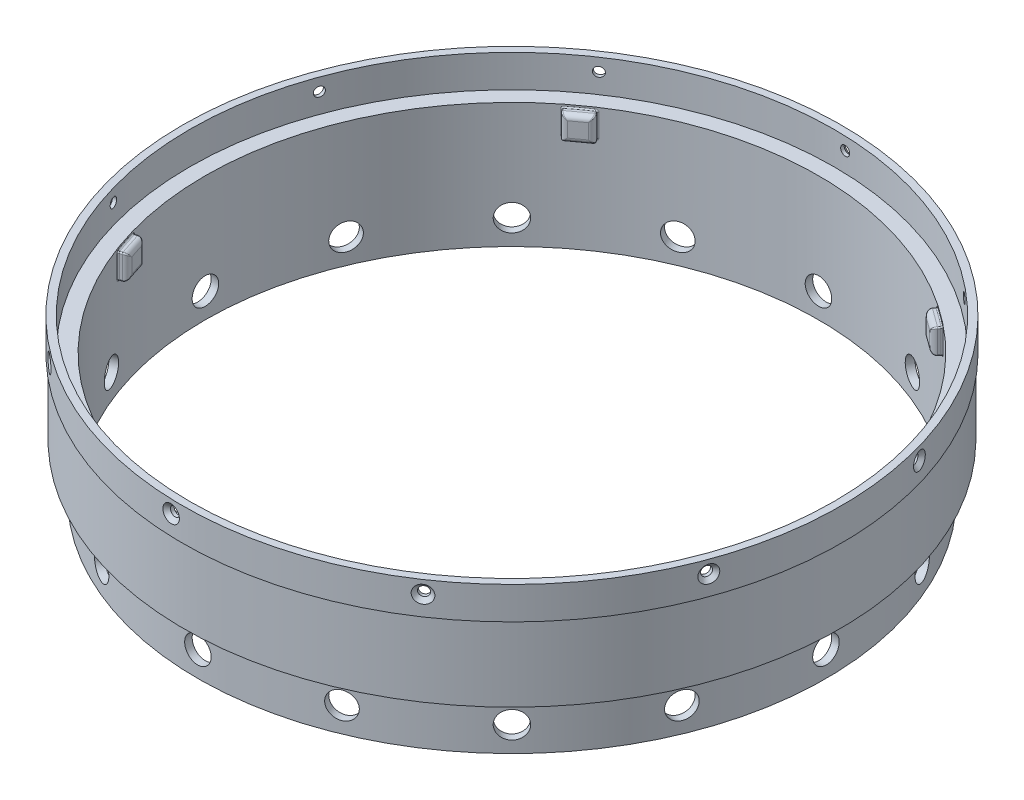
SolidWorks part; units mm, degrees
ref_plane "Front Plane" through (0, 0, 0) normal (0, 0, 1) x (1, 0, 0)
ref_plane "Top Plane" through (0, 0, 0) normal (0, 1, 0) x (1, 0, 0)
ref_plane "Right Plane" through (0, 0, 0) normal (1, 0, 0) x (0, 0, -1)
sketch "Sketch1" plane through (0, 0, 0) normal (0, 0, 1) x (1, 0, 0)
  line L0 (0, 49.1435) -> (0, -38.5417) construction
  line L1 (83.82, 42.3241) -> (83.82, 34.0691)
  line L2 (83.82, 34.0691) -> (83.439, 34.0691)
  line L3 (83.439, 34.0691) -> (83.439, 15.0191)
  line L4 (83.439, 15.0191) -> (79.9338, 15.0191)
  line L5 (79.9338, 15.0191) -> (79.9338, 2.3191)
  line L6 (79.9338, 2.3191) -> (78.0288, 2.3191)
  line L7 (78.0288, 2.3191) -> (78.0288, 34.0691)
  line L8 (78.0288, 34.0691) -> (81.9531, 34.0691)
  line L9 (81.9531, 34.0691) -> (81.9531, 42.3241)
  line L10 (81.9531, 42.3241) -> (83.82, 42.3241)
  point P15 (0, 0)
  dimension "D1" = 19.05
  dimension "D2" = 0.381
  dimension "D3" = 8.255
  dimension "D4" = 31.75
  dimension "D5" = 12.7
  dimension "D6" = 1.8669
  dimension "D7" = 1.905
  dimension "D8" = 83.82
  dimension "D9" = 3.5052
revolve "Revolve1" add sketch "Sketch1" angle 360 about L0
hole_wizard "CSK for M2 Flat Head Machine Screw1" positions "3DSketch2" profile "Sketch2" countersink size "M2" standard "ANSI Metric" end condition through all
sketch3d "3DSketch2"
  point P0 (80.574, 39.0781, -23.1003)
sketch "Sketch2" plane through (80.574, 39.0781, -23.1003) normal (0, 1, 0) x (-0.2756, 0, -0.9613)
  line L0 (0, 0) -> (0, 201.4765)
  line L1 (0, 201.4765) -> (1.2, 201.4765)
  line L2 (1.2, 201.4765) -> (1.2, 1)
  line L3 (1.2, 1) -> (2.2, 0)
  line L5 (2.2, 0) -> (0, 0)
  line L6 (-1.2, 1) -> (-2.2, 0) construction
  line L11 (0, -6.35) -> (0, 107.95) construction
  dimension "Thru Hole Dia." = 2.4
  dimension "Thru Hole Depth" = 201.4765
  dimension "Near C'Sink Dia." = 4.4
  dimension "Near C'Sink Angle" = 90
pattern_circular "CirPattern1" count 10 over 360 about axis through (0, 49.1435, 0) along (0, 1, 0) of "CSK for M2 Flat Head Machine Screw1"
sketch3d "3DSketch4"
  point P0 (-2.4273, 4.97, 79.8969)
ref_plane "Plane1" through (0, 0, 82.4369) normal (0, 0, 1) x (1, 0, 0)
hole_wizard "17/64 (0.26563) Diameter Hole1" positions "Sketch6" profile "Sketch7" hole size "17/64" standard "ANSI Inch" end condition through all
sketch "Sketch6" plane through (0, 0, 82.4369) normal (0, 0, 1) x (1, 0, 0)
  line L0 (-79.9338, 15.0191) -> (79.9338, 15.0191) construction
  point P0 (0, 8.6691)
  dimension "D1" = 6.35
sketch "Sketch7" plane through (0, 8.6691, 82.4369) normal (1, 0, 0) x (0, -1, 0)
  line L0 (0, 0) -> (0, 191.953)
  line L1 (0, 191.953) -> (3.3735, 191.953)
  line L2 (3.3735, 191.953) -> (3.3735, 0)
  line L5 (3.3735, 0) -> (0, 0)
  line L11 (0, -6.35) -> (0, 107.95) construction
  dimension "Thru Hole Dia." = 6.747
  dimension "Thru Hole Depth" = 191.953
pattern_circular "CirPattern2" count 16 over 360 about axis through (0, 49.1435, 0) along (0, 1, 0) of "17/64 (0.26563) Diameter Hole1"
ref_plane "Plane3" through (0, 0, 80.518) normal (0, 0, 1) x (1, 0, 0)
sketch "Sketch14" plane through (0, 0, 80.518) normal (0, 0, 1) x (1, 0, 0)
  line L1 (-3.175, 33.3424) -> (3.175, 33.3424)
  line L2 (-3.175, 33.3424) -> (-3.175, 26.9924)
  line L3 (-3.175, 26.9924) -> (3.175, 26.9924)
  line L4 (3.175, 33.3424) -> (3.175, 26.9924)
  line L5 (-3.175, 33.3424) -> (3.175, 26.9924) construction
  line L6 (-3.175, 26.9924) -> (3.175, 33.3424) construction
  point P0 (0, 30.1674)
  dimension "D1" = 6.35
extrude "Boss-Extrude1" add sketch "Sketch14" against normal blind 4.7625
fillet "Fillet1" radius 1.27 4 edges at (3.175, 30.1674, 75.7555) (0, 26.9924, 75.7555) (-3.175, 30.1674, 75.7555) (0, 33.3424, 75.7555)
fillet "Fillet2" radius 0.3175 8 edges at (-2.803, 27.3644, 76.1275) (2.803, 27.3644, 76.1275) (-2.803, 32.9705, 76.1275) (2.803, 32.9705, 76.1275) (-3.175, 26.9924, 77.4948) (3.175, 26.9924, 77.4948) (-3.175, 33.3424, 77.4948) (3.175, 33.3424, 77.4948)
fillet "Fillet3" radius 0.3175 8 edges at (-3.1055, 27.1117, 77.967) (-3.175, 30.1674, 77.9642) (-3.0559, 33.2728, 77.9689) (0, 33.3424, 78.0288) (3.1055, 33.2232, 77.967) (3.175, 30.1674, 77.9642) (3.0559, 27.0621, 77.9689) (0, 26.9924, 78.0288)
pattern_circular "CirPattern5" count 5 over 360 about axis through (0, 49.1435, 0) along (0, 1, 0) of "Boss-Extrude1", "Fillet3", "Fillet2", "Fillet1"
